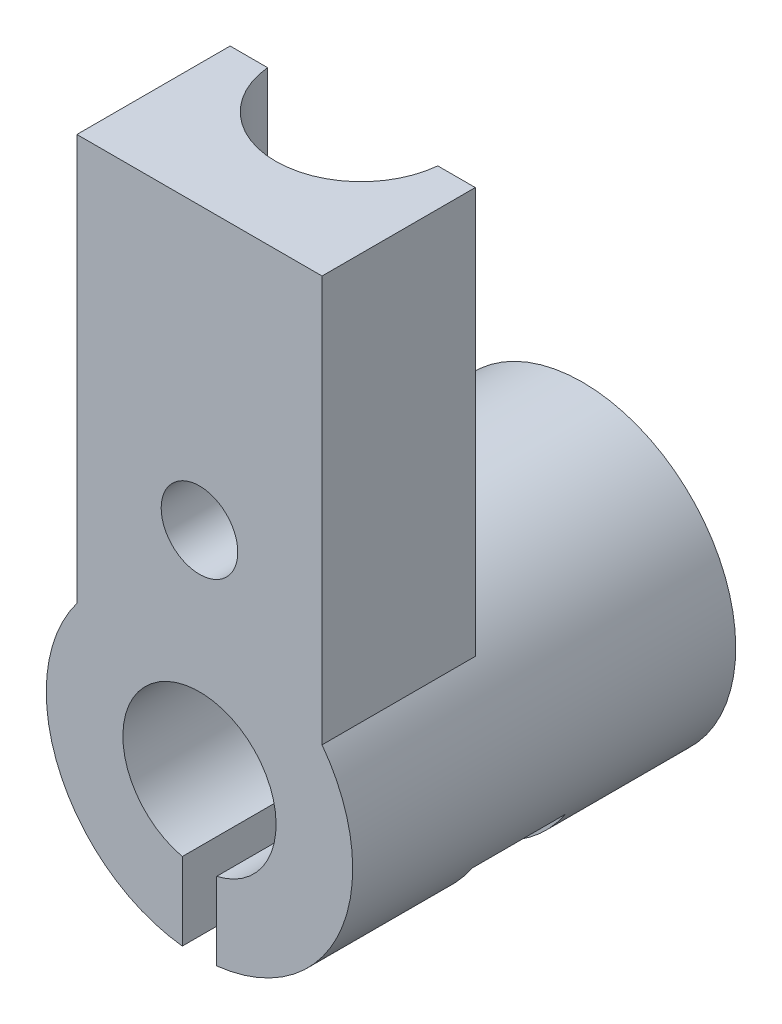
SolidWorks part; units mm, degrees
ref_plane "Front Plane" through (0, 0, 0) normal (0, 0, 1) x (1, 0, 0)
ref_plane "Top Plane" through (0, 0, 0) normal (0, 1, 0) x (1, 0, 0)
ref_plane "Right Plane" through (0, 0, 0) normal (1, 0, 0) x (0, 0, -1)
sketch "Sketch1" plane through (0, 0, 0) normal (0, 0, 1) x (1, 0, 0)
  circle A0 centre (0, 0) radius 20
  circle A1 centre (0, 0) radius 10
extrude "Boss-Extrude2" add sketch "Sketch1" along normal blind 50
ref_plane "Plane2" through (0, 65, 0) normal (0, 1, 0) x (1, 0, 0)
sketch "Sketch4" plane through (0, 65, 0) normal (0, 1, 0) x (1, 0, 0)
  line L0 (0, 4.4964) -> (0, -57.4728) construction
  line L1 (-20, -50) -> (20, -50) construction
  line L2 (-16, -30) -> (16, -30)
  line L3 (-16, -30) -> (-16, -50)
  line L4 (-16, -50) -> (16, -50)
  line L5 (16, -30) -> (16, -50)
  point P9 (0, -30)
  dimension "D1" = 20
  dimension "D2" = 32
extrude "Boss-Extrude3" add sketch "Sketch4" against normal up to surface (53 mm away)
sketch "Sketch5" plane through (0, 65, 0) normal (0, 1, 0) x (1, 0, 0)
  circle A0 centre (0, -28.9001) radius 11.1615
extrude "Cut-Extrude1" cut sketch "Sketch5" against normal blind 25
sketch "Sketch7" plane through (0, 0, 0) normal (0, 0, -1) x (-1, 0, 0)
  line L1 (-2.2409, -24.2648) -> (2.2409, -24.2648)
  line L2 (-2.2409, -24.2648) -> (-2.2409, -6.1014)
  line L3 (-2.2409, -6.1014) -> (2.2409, -6.1014)
  line L4 (2.2409, -24.2648) -> (2.2409, -6.1014)
  line L5 (-2.2409, -24.2648) -> (2.2409, -6.1014) construction
  line L6 (-2.2409, -6.1014) -> (2.2409, -24.2648) construction
  point P0 (0, -15.1831)
extrude "Cut-Extrude2" cut sketch "Sketch7" against normal through all
sketch "Sketch9" plane through (0, 0, 30) normal (0, 0, -1) x (-1, 0, 0)
  circle A0 centre (0, 28.2748) radius 5
extrude "Cut-Extrude3" cut sketch "Sketch9" against normal through all
sketch "Sketch10" plane through (0, 0, 0) normal (1, 0, 0) x (0, 0, -1)
  line L0 (-25, 4.2498) -> (-25, -28.2545) construction
  line L1 (-50, -19.8741) -> (0, -19.8741)
  line L2 (-50, -19.8741) -> (-50, -9.7457)
  line L4 (0, -19.8741) -> (0, -9.7457)
  line L6 (-31.124, -11.0735) -> (-18.876, -11.0735)
  line L7 (-31.124, -11.0735) -> (-31.124, -18.5735)
  line L8 (-31.124, -18.5735) -> (-18.876, -18.5735)
  line L9 (-18.876, -11.0735) -> (-18.876, -18.5735)
  point P12 (-25, -11.0735)
  dimension "D1" = 7.5
extrude "Cut-Extrude4" cut sketch "Sketch10" against normal blind 15 from offset 19 contours L6 L0 L8 L9 | L0 L6 L7 L8
mirror "Mirror1" about plane through (0, 0, 0) normal (1, 0, 0) of "Cut-Extrude4"
sketch "Sketch11" plane through (-4, 0, 0) normal (-1, 0, 0) x (0, 0, 1)
  line L0 (25, -11.0735) -> (25, -18.5735) construction
  line L1 (18.876, -11.0735) -> (31.124, -11.0735) construction
  line L2 (18.876, -18.5735) -> (31.124, -18.5735) construction
  circle A0 centre (25, -14.8235) radius 3
extrude "Cut-Extrude5" cut sketch "Sketch11" against normal through all
